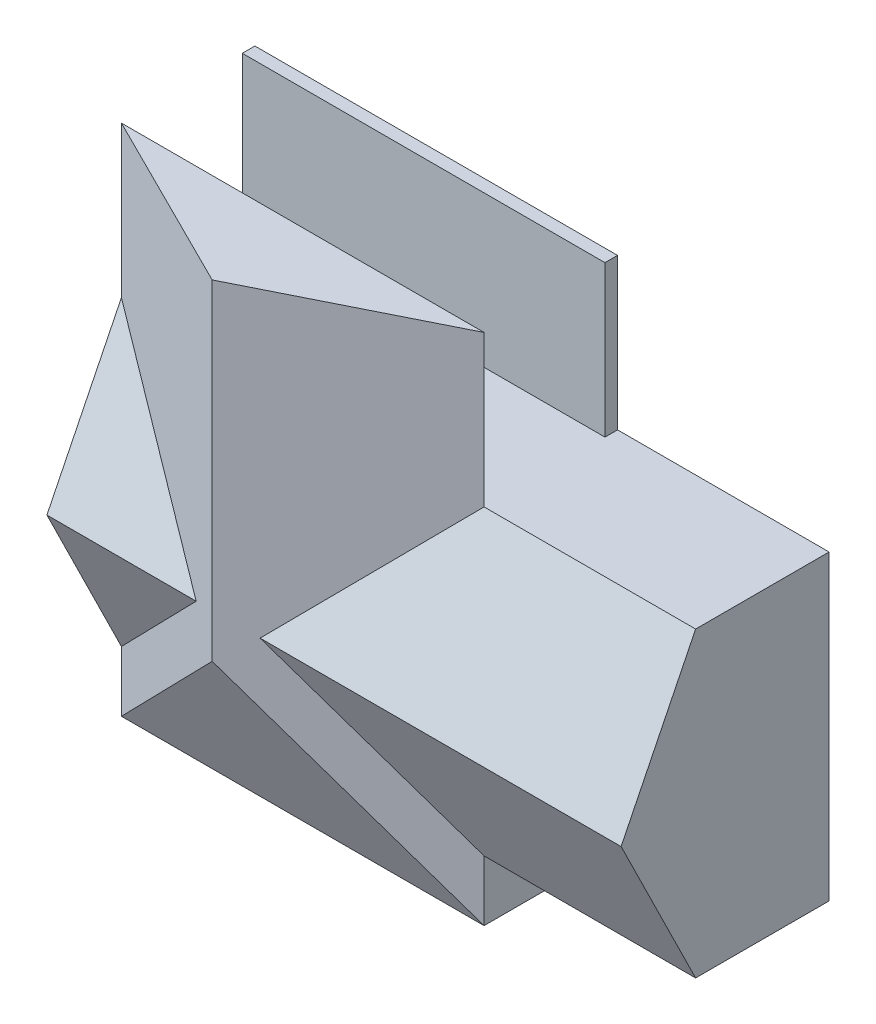
SolidWorks part; units mm, degrees
ref_plane "Front Plane" through (0, 0, 0) normal (0, 0, 1) x (1, 0, 0)
ref_plane "Top Plane" through (0, 0, 0) normal (0, 1, 0) x (1, 0, 0)
ref_plane "Right Plane" through (0, 0, 0) normal (1, 0, 0) x (0, 0, -1)
sketch "Sketch3" plane through (0, 0, 0) normal (0, 0, 1) x (1, 0, 0)
  line L0 (152.4, 152.4) -> (4550.005, 152.4)
  line L1 (0, 0) -> (11582.4, 0)
  line L2 (0, 0) -> (0, 6096)
  line L3 (0, 6096) -> (11582.4, 6096)
  line L4 (11582.4, 0) -> (11582.4, 6096)
  line L5 (4550.005, 152.4) -> (4550.005, 2596.7986)
  line L6 (4550.005, 2596.7986) -> (5842, 2596.7986)
  line L7 (11582.4, 6096) -> (7620, 6096) construction
  line L8 (7620, 6096) -> (5842, 6096) construction
  line L9 (5842, 5943.6) -> (5842, 3511.1986)
  line L10 (5943.6, 3511.1986) -> (10284.7543, 3511.1986)
  line L11 (7620, 5943.6) -> (7620, 3612.7986)
  line L12 (4550.005, 2596.7986) -> (5842, 2596.7986) construction
  line L13 (7315.2, 2495.1986) -> (7315.2, 152.4)
  line L14 (5842, 3511.1986) -> (5842, 2596.7986)
  line L15 (10386.3543, 3511.1986) -> (10386.3543, 2596.7986)
  line L16 (9786.5812, 3511.1986) -> (9786.5812, 2596.7986) construction
  line L17 (0, 6096) -> (0, 9448.8) construction
  line L18 (0, 9448.8) -> (6388.492, 9448.8) construction
  line L19 (6388.492, 9448.8) -> (6388.492, 6096) construction
  line L20 (11430, 152.4) -> (11430, 2495.1986)
  line L21 (3310.1163, 2590.8) -> (0, 2590.8) construction
  line L22 (152.4, 5943.6) -> (5842, 5943.6)
  line L23 (152.4, 152.4) -> (152.4, 5943.6)
  line L24 (4651.605, 152.4) -> (4651.605, 2495.1986)
  line L25 (4651.605, 2495.1986) -> (7315.2, 2495.1986)
  line L26 (7416.8, 2495.1986) -> (7416.8, 152.4)
  line L27 (10284.7543, 3511.1986) -> (10284.7543, 2596.7986)
  line L28 (5943.6, 3612.7986) -> (7620, 3612.7986)
  line L29 (5943.6, 5943.6) -> (5943.6, 3612.7986)
  line L30 (7721.6, 5943.6) -> (7721.6, 3612.7986)
  line L31 (7620, 6096) -> (7620, 3505.2) construction
  line L32 (7721.6, 6096) -> (7721.6, 3505.2) construction
  line L33 (5842, 6096) -> (5842, 3511.1986) construction
  line L34 (5943.6, 6096) -> (5943.6, 3511.1986) construction
  line L35 (5943.6, 5943.6) -> (7620, 5943.6)
  line L36 (152.4, 5943.6) -> (11430, 5943.6) construction
  line L37 (7721.6, 5943.6) -> (11430, 5943.6)
  line L38 (5842, 3612.7986) -> (11582.4, 3612.7986) construction
  line L39 (7721.6, 3612.7986) -> (11430, 3612.7986)
  line L40 (11430, 3612.7986) -> (11430, 5943.6)
  line L41 (11430, 152.4) -> (11430, 5943.6) construction
  line L42 (5842, 3511.1986) -> (11582.4, 3511.1986) construction
  line L43 (10386.3543, 3511.1986) -> (11430, 3511.1986)
  line L44 (10386.3543, 2596.7986) -> (11430, 2596.7986)
  line L45 (4550.005, 2596.7986) -> (11582.4, 2596.7986) construction
  line L46 (11430, 2596.7986) -> (11430, 3511.1986)
  line L47 (4651.605, 2495.1986) -> (11582.4, 2495.1986) construction
  line L48 (7315.2, 2596.7986) -> (7315.2, 0) construction
  line L49 (7416.8, 2596.7986) -> (7416.8, 0) construction
  line L50 (7416.8, 2495.1986) -> (11430, 2495.1986)
  line L51 (7416.8, 152.4) -> (11430, 152.4)
  line L52 (152.4, 152.4) -> (11430, 152.4) construction
  line L53 (4550.005, 0) -> (4550.005, 2596.7986) construction
  line L54 (4651.605, 0) -> (4651.605, 2495.1986) construction
  line L55 (4651.605, 152.4) -> (7315.2, 152.4)
  line L56 (5943.6, 3511.1986) -> (5943.6, 2596.7986)
  line L57 (5943.6, 2596.7986) -> (10284.7543, 2596.7986)
  line L58 (5943.6, 2596.7986) -> (7315.2, 2596.7986) construction
  dimension "D1" = 11582.4
  dimension "D2" = 6096
  dimension "D4" = 3962.4
  dimension "D5" = 1778
  dimension "D7" = 914.4
  dimension "D8" = 152.4
  dimension "D9" = 101.6
  dimension "D10" = 101.6
  dimension "D11" = 101.6
  dimension "D12" = 101.6
  dimension "D13" = 101.6
extrude "Boss-Extrude1" add sketch "Sketch3" along normal blind 2438.4 contours L1 L4 L3 L2 L55 L24 L25 L13 L51 L26 L50 L20 L46 L44 L15 L43 L40 L39 L30 L37 L10 L27 L6 L5 L0 L23 L22 L9 L29 L35 L11 L28
sketch "Sketch4" plane through (0, 0, 0) normal (0, 0, -1) x (-1, 0, 0)
  line L1 (-11582.4, 6096) -> (0, 6096)
  line L2 (-11582.4, 6096) -> (-11582.4, 0)
  line L3 (-11582.4, 0) -> (0, 0)
  line L4 (0, 6096) -> (0, 0)
extrude "Boss-Extrude2" add sketch "Sketch4" along normal blind 254
sketch "Sketch5" plane through (0, 0, 0) normal (0, 0, 1) x (1, 0, 0)
  line L1 (3330.805, 2596.7986) -> (152.4, 2596.7986)
  line L2 (152.4, 152.4) -> (152.4, 5943.6) construction
  line L3 (152.4, 2596.7986) -> (152.4, 2495.1986)
  line L4 (152.4, 152.4) -> (152.4, 5943.6) construction
  line L5 (152.4, 2495.1986) -> (3330.805, 2495.1986)
  line L6 (3330.805, 2495.1986) -> (3330.805, 2596.7986)
extrude "Boss-Extrude3" add sketch "Sketch5" along normal blind 1016
sketch "Sketch6" plane through (0, 0, 0) normal (-1, 0, 0) x (0, 0, 1)
  line L0 (2438.4, 6096) -> (2438.4, 0)
  line L1 (2438.4, 6096) -> (3941.5073, 3048)
  line L2 (2438.4, 3048) -> (3941.5073, 3048) construction
  line L3 (3941.5073, 3048) -> (2438.4, 0)
  dimension "D1" = 26.25
extrude "Boss-Extrude4" add sketch "Sketch6" against normal up to surface (11582.4 mm away) up to face at (11582.4, 3048, 1092.2)
sketch "Sketch7" plane through (0, 6096, 0) normal (0, 1, 0) x (1, 0, 0)
  line L0 (0, 254) -> (7315.2, 254) construction
  line L1 (0, 254) -> (11582.4, 254) construction
  line L2 (7315.2, 254) -> (7315.2, -2438.4) construction
  line L3 (0, -2438.4) -> (11582.4, -2438.4) construction
  line L4 (7937.8596, -2438.4) -> (5791.2, -3941.5073)
  line L5 (11582.4, -3941.5073) -> (0, -3941.5073) construction
  line L6 (5791.2, -3941.5073) -> (5791.2, -2438.4) construction
  line L7 (3644.5404, -2438.4) -> (5791.2, -3941.5073)
  line L8 (7937.8596, -2438.4) -> (3644.5404, -2438.4)
  dimension "D1" = 55
sketch "Sketch8" plane through (0, 0, -254) normal (0, 0, -1) x (-1, 0, 0)
  line L1 (0, 6096) -> (-7315.2, 6096)
  line L2 (0, 6096) -> (0, 9144)
  line L3 (0, 9144) -> (-7315.2, 9144)
  line L4 (-7315.2, 6096) -> (-7315.2, 9144)
  dimension "D1" = 7315.2
  dimension "D2" = 3048
extrude "Boss-Extrude6" add sketch "Sketch8" against normal blind 254 separate body
sketch "Sketch9" plane through (0, 0, 0) normal (-1, 0, 0) x (0, 0, 1)
  line L0 (2438.4, 0) -> (4693.0609, 4572)
  line L1 (2438.4, 0) -> (2438.4, 9144)
  line L2 (2438.4, 4572) -> (4693.0609, 4572) construction
  line L3 (2438.4, 9144) -> (4693.0609, 4572)
sketch "Sketch10" plane through (0, 9144, 0) normal (0, 1, 0) x (1, 0, 0)
  line L0 (7315.2, -2438.4) -> (0, -2438.4)
  line L1 (3644.5404, -2438.4) -> (3657.6, -4693.0609) construction
  line L2 (7315.2, -4693.0609) -> (0, -4693.0609) construction
  line L5 (7315.2, -2438.4) -> (3655.1104, -4263.2533)
  line L6 (3655.1104, -4263.2533) -> (0, -2438.4)
  dimension "D1" = 26.5
extrude "Boss-Extrude7" add sketch "Sketch10" against normal blind 10363.2
sketch "Sketch11" plane through (0, -967.2564, 1961.4019) normal (0, -0.4423, 0.8969) x (1, 0, 0)
  line L1 (5444.9184, 4256.1108) -> (2083.927, 4256.1108)
  line L2 (5444.9184, 4256.1108) -> (5444.9184, 5301.5124)
  line L3 (5444.9184, 5301.5124) -> (2083.927, 5301.5124)
  line L4 (2083.927, 4256.1108) -> (2083.927, 5301.5124)
extrude "Cut-Extrude1" [suppressed] cut sketch "Sketch11" along normal blind 6085.84
sketch "Sketch12" plane through (0, 0, -254) normal (0, 0, -1) x (-1, 0, 0)
  line L0 (0, 0) -> (0, -1219.2)
  line L1 (0, -1219.2) -> (-7315.2, -1219.2)
  line L2 (-7315.2, -1219.2) -> (-7315.2, 0)
  line L3 (-11582.4, 0) -> (0, 0) construction
  line L4 (-7315.2, 0) -> (0, 0)
extrude "Boss-Extrude8" add sketch "Sketch12" against normal blind 2692.4
sketch "Sketch14" plane through (0, 0, 0) normal (-1, 0, 0) x (0, 0, 1)
  line L0 (2916.7919, -235.9168) -> (4419.8992, 2812.0832)
  line L1 (2916.7919, -235.9168) -> (2299.5618, -1487.5356)
  line L2 (4419.8992, 2812.0832) -> (4384.9984, -1487.5356)
  line L3 (4384.9984, -1487.5356) -> (2299.5618, -1487.5356)
  line L6 (-254, 6096) -> (-254, -1219.2)
  line L7 (-254, -1219.2) -> (2438.4, -1219.2)
  line L8 (2438.4, -1219.2) -> (2438.4, 0)
  line L9 (2438.4, 0) -> (3941.5073, 3048)
  line L10 (3941.5073, 3048) -> (2438.4, 6096)
  line L11 (2438.4, 6096) -> (-254, 6096)
  line L15 (2438.4, 0) -> (3941.5073, 3048) construction
  dimension "D1" = 0
  dimension "D2" = 533.4
extrude "Cut-Extrude2" [suppressed] cut sketch "Sketch14" against normal blind 8897.366
sketch "Sketch15" plane through (0, -1219.2, 0) normal (0, -1, 0) x (1, 0, 0)
  line L0 (0, 2438.4) -> (7315.2, 2438.4) construction
  line L1 (3657.6, 2438.4) -> (3657.6, 3352.8) construction
  line L2 (2641.6, 2438.4) -> (4673.6, 2438.4)
  line L3 (4673.6, 2438.4) -> (3657.6, 3352.8)
  line L4 (3657.6, 3352.8) -> (2641.6, 2438.4)
  point P9 (3657.6, 2438.4)
extrude "Boss-Extrude9" add sketch "Sketch15" along normal blind 1219.2
ref_plane "Plane1" through (0, -1205.7554, 2445.0301) normal (0, -0.4423, 0.8969) x (1, 0, 0)
sketch "Sketch16" plane through (0, -1205.7554, 2445.0301) normal (0, -0.4423, 0.8969) x (1, 0, 0)
  line L1 (7603.0974, 4283.6963) -> (-536.5988, 4283.6963)
  line L2 (7603.0974, 4283.6963) -> (7603.0974, -1196.5845)
  line L3 (7603.0974, -1196.5845) -> (-536.5988, -1196.5845)
  line L4 (-536.5988, 4283.6963) -> (-536.5988, -1196.5845)
extrude "Cut-Extrude3" cut sketch "Sketch16" along normal blind 2099.564
